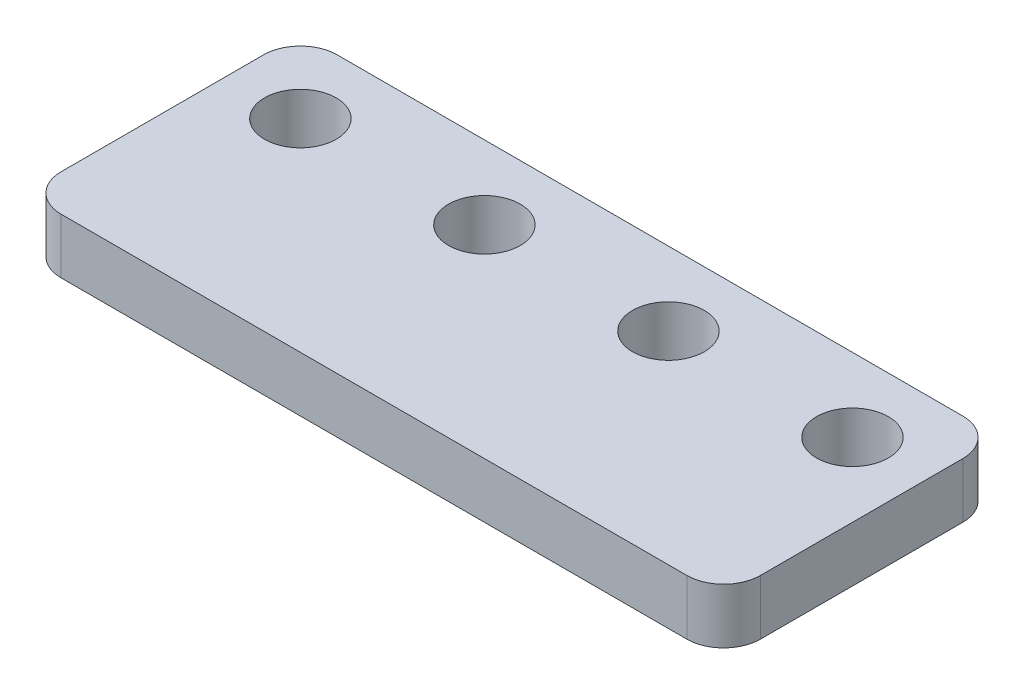
SolidWorks part; units mm, degrees
ref_plane "Front Plane" through (0, 0, 0) normal (0, 0, 1) x (1, 0, 0)
ref_plane "Top Plane" through (0, 0, 0) normal (0, 1, 0) x (1, 0, 0)
ref_plane "Right Plane" through (0, 0, 0) normal (1, 0, 0) x (0, 0, -1)
sketch "Sketch1" plane through (0, 0, 0) normal (0, 1, 0) x (1, 0, 0)
  line L1 (-36, 0) -> (-2, 0)
  line L2 (-38, -2) -> (-38, -13)
  line L3 (-36, -15) -> (-2, -15)
  line L4 (0, -2) -> (0, -13)
  arc A0 (-2, -15) -> (0, -13) centre (-2, -13) ccw
  arc A1 (-38, -13) -> (-36, -15) centre (-36, -13) ccw
  arc A2 (-36, 0) -> (-38, -2) centre (-36, -2) ccw
  arc A3 (-2, 0) -> (0, -2) centre (-2, -2) cw
  point P7 (0, -15)
  point P12 (-38, 0)
  point P15 (0, 0)
  dimension "D3" = 2
  dimension "D1" = 38
  dimension "D2" = 15
extrude "Boss-Extrude1" add sketch "Sketch1" along normal blind 3
sketch "Sketch2" plane through (0, 3, 0) normal (0, 1, 0) x (1, 0, 0)
  line L2 (-4, -4) -> (-54, -4) construction
  line L10 (-2, 0) -> (-36, 0) construction
  line L11 (0, -13) -> (0, -2) construction
  circle A20 centre (-4, -4) radius 1.95
  circle A21 centre (-14, -4) radius 1.95
  circle A22 centre (-24, -4) radius 1.95
  circle A23 centre (-54, -4) radius 1.95
  circle A24 centre (-34, -4) radius 1.95
  circle A25 centre (-44, -4) radius 1.95
  dimension "D1" = 4
  dimension "D4" = 10
  dimension "D7" = 3.9
  dimension "D8" = 3.9
  dimension "D9" = 3.9
  dimension "D10" = 3.9
  dimension "D11" = 10
  dimension "D12" = 10
  dimension "D13" = 10
  dimension "D5" = 3.9
  dimension "D6" = 3.9
  dimension "D2" = 4
  dimension "D3" = 10
extrude "Cut-Extrude1" cut sketch "Sketch2" against normal through all
